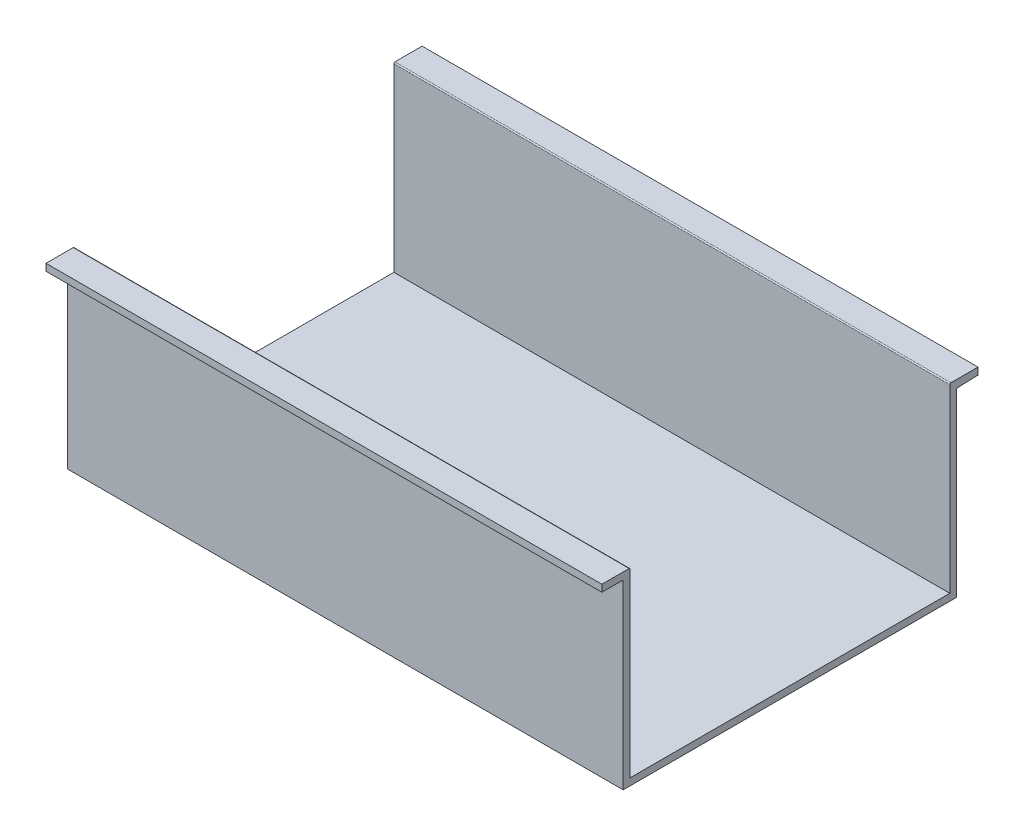
SolidWorks part; units mm, degrees
ref_plane "Front Plane" through (0, 0, 0) normal (0, 0, 1) x (1, 0, 0)
ref_plane "Top Plane" through (0, 0, 0) normal (0, 1, 0) x (1, 0, 0)
ref_plane "Right Plane" through (0, 0, 0) normal (1, 0, 0) x (0, 0, -1)
sketch "Sketch1" plane through (0, 0, 0) normal (1, 0, 0) x (0, 0, -1)
  line L0 (5, -5) -> (5, -125.2708)
  line L2 (0, -0.2708) -> (0, -130.2708)
  line L3 (0, -130.2708) -> (240, -130.2708)
  line L4 (240, -0.8) -> (240, -130.2708)
  line L5 (5, -125.2708) -> (235, -125.2708)
  line L6 (235, -5) -> (235, -125.2708)
  line L8 (0, 0) -> (240, 0) construction
  line L9 (5, -5) -> (235, -5) construction
  line L10 (-0.8, 0.5292) -> (-15.3159, 0.5292)
  line L11 (-15.3159, 0.5292) -> (-15.3159, 5.5292)
  line L12 (-15.3159, 5.5292) -> (4.2, 5.5292)
  line L13 (5, 4.7292) -> (5, -5)
  line L14 (120, -130.2708) -> (120, -14.8256) construction
  line L15 (235, 4.7292) -> (235, -5)
  line L16 (255.3159, 0.5292) -> (255.3159, 5.5292)
  line L17 (240.7709, -0.0005) -> (255.3159, 0.5292)
  line L18 (255.3159, 5.5292) -> (235.8, 5.5292)
  line L19 (240, 0) -> (240, -130.2708) construction
  line L20 (0, 0) -> (0, -130.2708) construction
  arc A0 (235, 4.7292) -> (235.8, 5.5292) centre (235.8, 4.7292) cw
  arc A1 (240.7709, -0.0005) -> (240, -0.8) centre (240.8, -0.8) ccw
  arc A2 (-0.8, 0.5292) -> (0, -0.2708) centre (-0.8, -0.2708) cw
  arc A3 (4.2, 5.5292) -> (5, 4.7292) centre (4.2, 4.7292) cw
  point P19 (235, 5.5292)
  point P28 (5, 5.5292)
  point P29 (-15.3159, 0.5292)
  dimension "D5" = 0.8
  dimension "D1" = 130
  dimension "D2" = 240
  dimension "D4" = 5
  dimension "D3" = 5
extrude "Boss-Extrude1" add sketch "Sketch1" along normal blind 400
